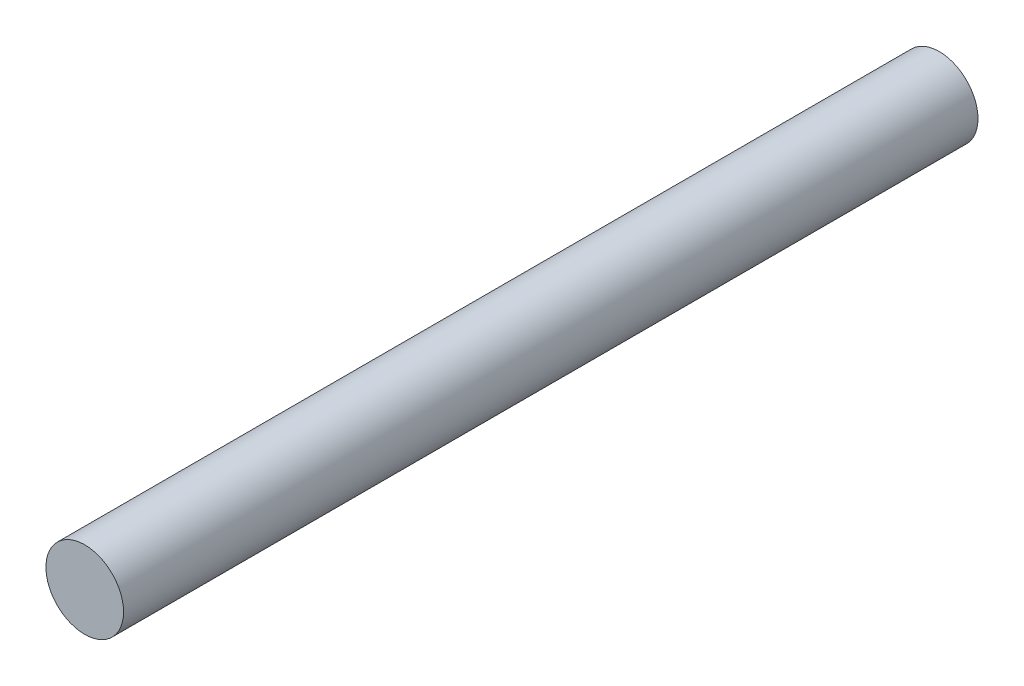
SolidWorks part; units mm, degrees
ref_plane "Front Plane" through (0, 0, 0) normal (0, 0, 1) x (1, 0, 0)
ref_plane "Top Plane" through (0, 0, 0) normal (0, 1, 0) x (1, 0, 0)
ref_plane "Right Plane" through (0, 0, 0) normal (1, 0, 0) x (0, 0, -1)
sketch "Sketch2" plane through (0, 0, 0) normal (0, 0, 1) x (1, 0, 0)
  circle A0 centre (0, 0) radius 15.9
extrude "Boss-Extrude1" add sketch "Sketch2" along normal blind 350
